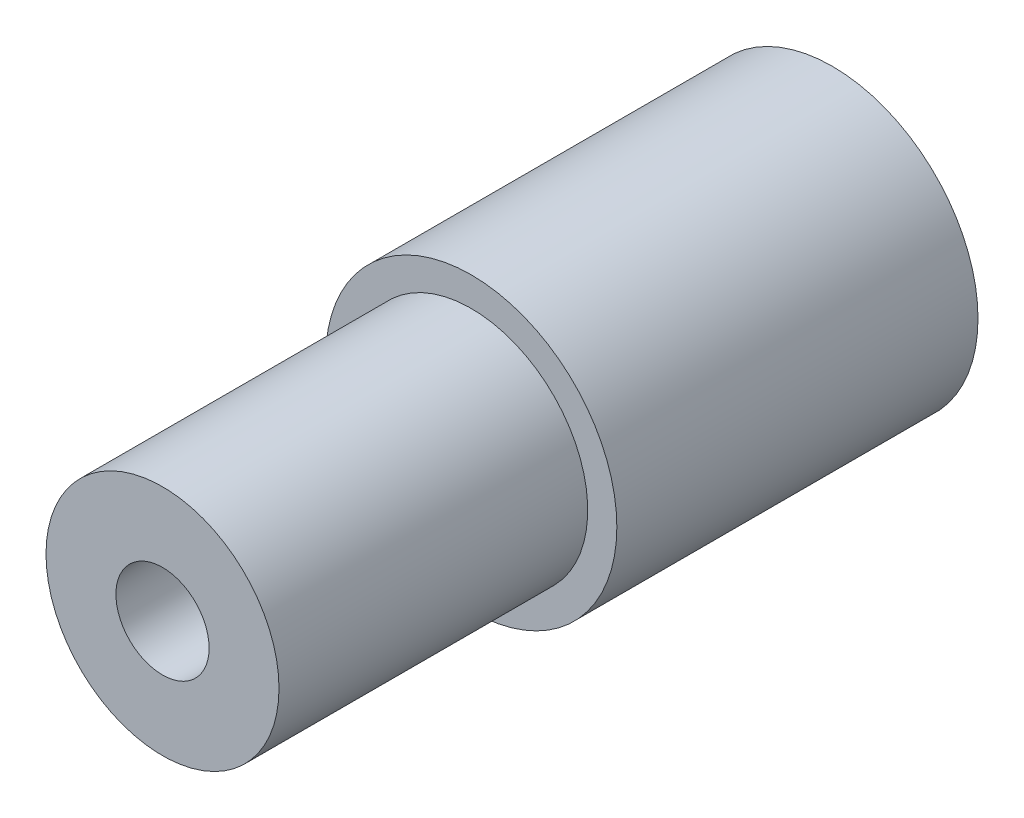
SolidWorks part; units mm, degrees
material "3003 Alloy"
ref_plane "Front Plane" through (0, 0, 0) normal (0, 0, 1) x (1, 0, 0)
ref_plane "Top Plane" through (0, 0, 0) normal (0, 1, 0) x (1, 0, 0)
ref_plane "Right Plane" through (0, 0, 0) normal (1, 0, 0) x (0, 0, -1)
sketch "Sketch2" plane through (0, 0, 0) normal (0, 0, 1) x (1, 0, 0)
  circle A0 centre (0, 0) radius 4
  circle A1 centre (0, 0) radius 1.6
  dimension "D1" = 8
  dimension "D2" = 3.2
extrude "Boss-Extrude1" add sketch "Sketch2" along normal blind 23
sketch "Sketch3" plane through (0, 0, 0) normal (0, 0, -1) x (-1, 0, 0)
  circle A0 centre (0, 0) radius 4 construction
  circle A1 centre (0, 0) radius 4
  circle A2 centre (0, 0) radius 5
  dimension "D1" = 10
extrude "Boss-Extrude2" add sketch "Sketch3" against normal blind 12.4
